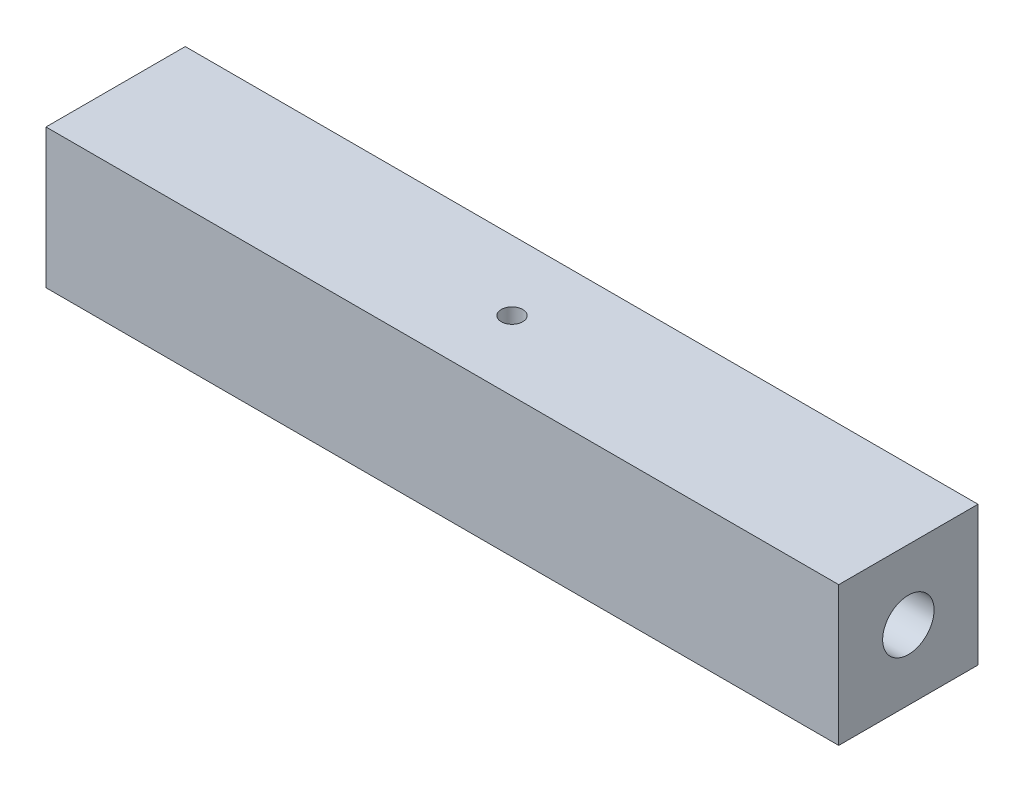
SolidWorks part; units mm, degrees
material "Oak"
ref_plane "Front Plane" through (0, 0, 0) normal (0, 0, 1) x (1, 0, 0)
ref_plane "Top Plane" through (0, 0, 0) normal (0, 1, 0) x (1, 0, 0)
ref_plane "Right Plane" through (0, 0, 0) normal (1, 0, 0) x (0, 0, -1)
sketch "Sketch1" plane through (0, 0, 0) normal (1, 0, 0) x (0, 0, -1)
  line L1 (-8.255, 8.255) -> (8.255, 8.255)
  line L2 (-8.255, 8.255) -> (-8.255, -8.255)
  line L3 (-8.255, -8.255) -> (8.255, -8.255)
  line L4 (8.255, 8.255) -> (8.255, -8.255)
  line L5 (-8.255, 8.255) -> (8.255, -8.255) construction
  line L6 (-8.255, -8.255) -> (8.255, 8.255) construction
  point P0 (0, 0)
  dimension "D1" = 16.51
  dimension "D2" = 16.51
extrude "Boss-Extrude1" add sketch "Sketch1" along normal mid plane 93.98
sketch "Sketch2" plane through (46.99, 0, 0) normal (1, 0, 0) x (0, 0, -1)
  circle A0 centre (0, 0) radius 3.048
  dimension "D1" = 6.096
extrude "Cut-Extrude1" cut sketch "Sketch2" against normal blind 17.78
mirror "Mirror1" about plane through (0, 0, 0) normal (1, 0, 0) of "Cut-Extrude1"
sketch "Sketch3" plane through (0, 0, 0) normal (0, 1, 0) x (1, 0, 0)
  circle A0 centre (0, 0) radius 1.27
extrude "Cut-Extrude2" cut sketch "Sketch3" against normal through all from surface at 8.255 starting at face at (0, 8.255, 0)
